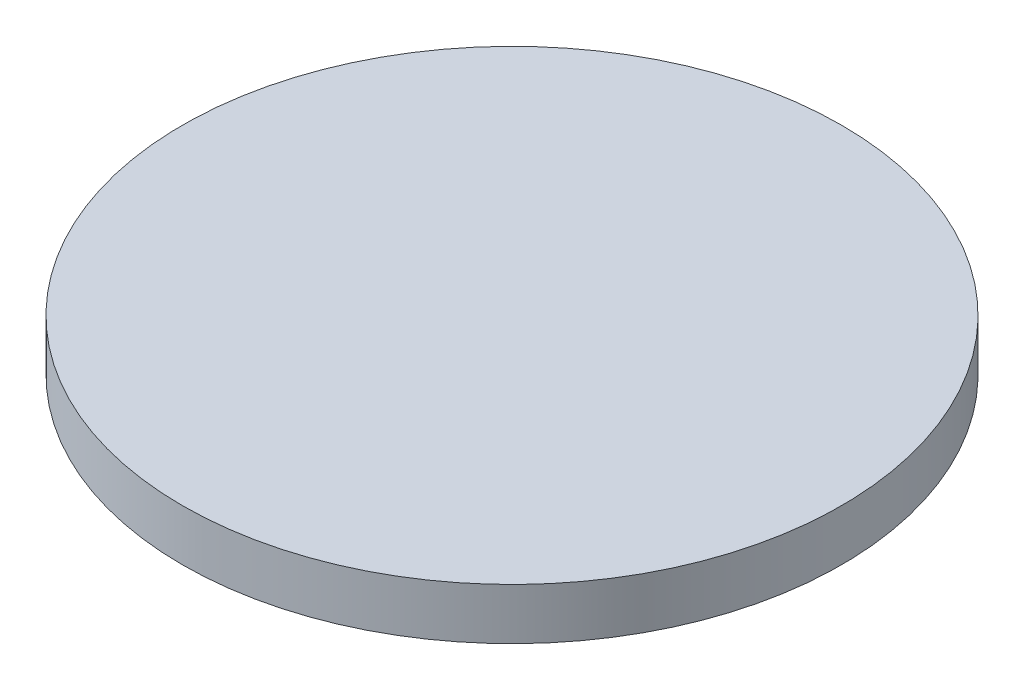
SolidWorks part; units mm, degrees
ref_plane "Front Plane" through (0, 0, 0) normal (0, 0, 1) x (1, 0, 0)
ref_plane "Top Plane" through (0, 0, 0) normal (0, 1, 0) x (1, 0, 0)
ref_plane "Right Plane" through (0, 0, 0) normal (1, 0, 0) x (0, 0, -1)
sketch "Sketch1" plane through (0, 0, 0) normal (0, 1, 0) x (1, 0, 0)
  circle A0 centre (0, 0) radius 114.3
  dimension "D1" = 228.6
extrude "Boss-Extrude1" add sketch "Sketch1" along normal blind 17.78
